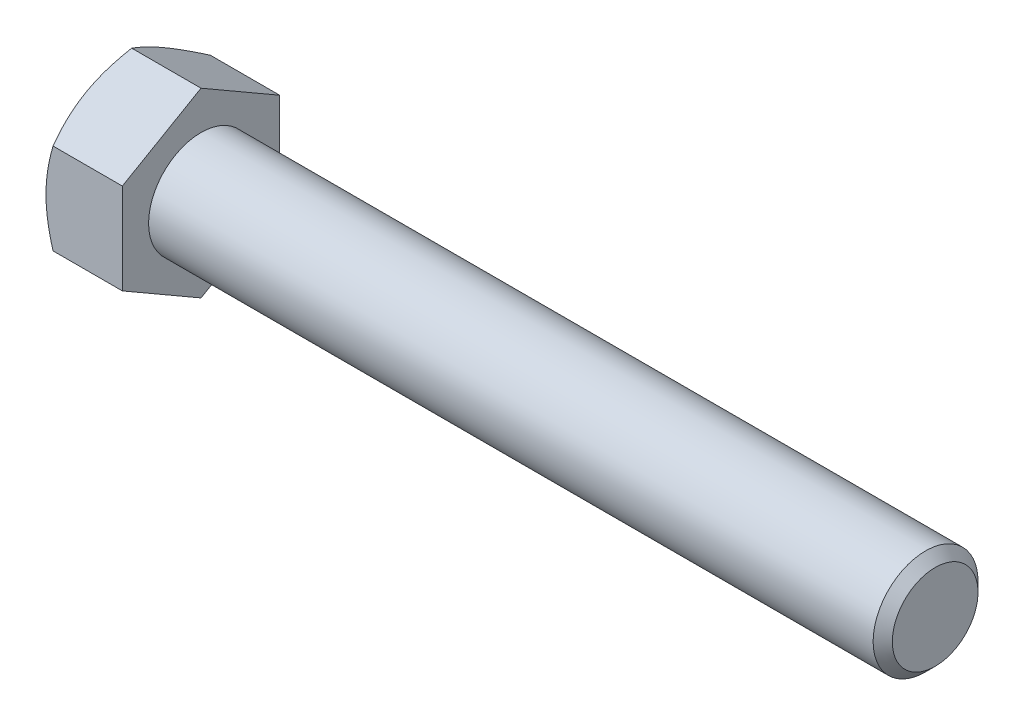
SolidWorks part; units mm, degrees
ref_plane "Plane1" through (0, 0, 0) normal (0, 0, 1) x (1, 0, 0)
ref_plane "Plane2" through (0, 0, 0) normal (0, 1, 0) x (1, 0, 0)
ref_plane "Plane3" through (0, 0, 0) normal (1, 0, 0) x (0, 0, -1)
sketch "Sketch1" plane through (0, 0, 0) normal (1, 0, 0) x (0, 0, -1)
  line L0 (9.525, 5.4993) -> (9.525, -5.4993)
  line L1 (-9.525, 5.4993) -> (-9.525, -5.4993)
  line L2 (9.525, -5.4993) -> (0, -10.9985)
  line L3 (0, -10.9985) -> (-9.525, -5.4993)
  line L4 (9.525, 5.4993) -> (0, 10.9985)
  line L5 (0, 10.9985) -> (-9.525, 5.4993)
  dimension "Width_flats" = 19.05
  dimension "D2" = 120
  dimension "D3" = 9.525
  dimension "D4" = 9.525
  dimension "D5" = 9.525
extrude "BaseHead" add sketch "Sketch1" along normal blind 9.2456
sketch "BodySke" plane through (0, 0, 0) normal (0, 0, 1) x (1, 0, 0)
  line L0 (0, 5.4993) -> (0, -5.4993) construction
  line L1 (0, 0) -> (98.1456, 0)
  line L2 (0, 0) -> (0, 6.35)
  line L3 (0, 6.35) -> (96.9823, 6.35)
  line L4 (98.1456, 0) -> (98.1456, 5.1867)
  line L5 (9.2456, 10.9985) -> (9.2456, 5.4993) construction
  line L6 (98.1456, 5.1867) -> (96.9823, 6.35)
  line L7 (0, 0) -> (96.52, 0) construction
  line L8 (98.1456, -5.1867) -> (96.9823, -6.35) construction
  line L9 (0, -6.35) -> (96.9823, -6.35) construction
  line L10 (11.1989, 15.24) -> (11.1989, -2.54) construction
  line L11 (66.3956, 15.24) -> (66.3956, -2.54) construction
  line L12 (9.2456, 5.4993) -> (9.2456, -5.4993) construction
  dimension "Length" = 88.9
  dimension "Body_ch_ang" = 45
  dimension "Diameter" = 12.7
  dimension "Minor_dia" = 10.3734
  dimension "Advance" = 1.9533
  dimension "Thread_nom" = 31.75
revolve "BaseBody" add sketch "BodySke" angle 360 about L7
cosmetic thread "ThreadCosmetic" parameters "Thread_length"=31.75, "Thread_minor"=10.3734
sketch "Sketch3" plane through (0, 0, 0) normal (0, 0, 1) x (1, 0, 0)
  line L0 (0, 9.525) -> (4.5169, 17.3485)
  line L1 (0, 10.9985) -> (0, 5.4993) construction
  line L2 (4.5169, 17.3485) -> (4.5169, 23.6985)
  line L3 (4.5169, 23.6985) -> (-12.7, 23.6985)
  line L4 (-12.7, 23.6985) -> (-12.7, 9.525)
  line L5 (-12.7, 9.525) -> (0, 9.525)
  line L6 (0, 0) -> (99.06, 0) construction
  line L7 (9.2456, 10.9985) -> (0, 10.9985) construction
  dimension "D1" = 9.525
  dimension "D2" = 6.35
  dimension "D3" = 12.7
  dimension "D4" = 6.35
  dimension "Head_ch_ang" = 30
revolve "HeadChamfer" cut sketch "Sketch3" angle 360 about L6
fillet "HeadFillet" [suppressed] radius 0.762
sketch "ThdSchSke" plane through (0, 0, 0) normal (0, 0, 1) x (1, 0, 0)
  line L0 (66.3956, -5.1867) -> (65.581, -6.35)
  line L1 (66.3956, -5.1867) -> (67.2102, -6.35)
  line L2 (67.2102, -6.35) -> (67.2102, -7.9375)
  line L3 (-3.175, 0) -> (5.1513, 0) construction
  line L5 (67.2102, -7.9375) -> (65.581, -7.9375)
  line L6 (65.581, -7.9375) -> (65.581, -6.35)
  dimension "Thread_minor" = 10.3734
  dimension "Diameter" = 12.7
  dimension "Start" = 66.3956
  dimension "SideAngle" = 55
  dimension "VeeAngle" = 70
  dimension "Overcut" = 15.875
revolve "ThreadSchematic" [suppressed] cut sketch "ThdSchSke" angle 360 about L3
pattern_linear "ThdSchPat" [suppressed]
equation "\"D3@Sketch1\" = \"Width_flats@Sketch1\" / 2"
equation "\"D4@Sketch1\" = \"D3@Sketch1\""
equation "\"D5@Sketch1\" = \"D4@Sketch1\""
equation "\"Thread_minor@ThreadCosmetic\" = \"Minor_dia@BodySke\""
equation "\"D1@Sketch3\" = \"Width_flats@Sketch1\" / 2"
equation "\"Thread_length@ThreadCosmetic\" = ((sgn( (\"Length@BodySke\" - \"Advance@BodySke\" ) - \"Thread_nom@BodySke\" )-1)*( (\"Length@BodySke\" - \"Advance@BodySke\" ) - \"Thread_nom@BodySke\" ))/-2+ \"Thread_nom@BodySke\""
equation "\"Thread_minor@ThdSchSke\" = \"Minor_dia@BodySke\""
equation "\"Diameter@ThdSchSke\" = \"Diameter@BodySke\""
equation "\"Overcut@ThdSchSke\" = \"Diameter@BodySke\" * 1.25"
equation "\"Start@ThdSchSke\" = \"Head_ht@BaseHead\" + \"Length@BodySke\" - \"Thread_length@ThreadCosmetic\"  '---Non-countersunk---"
equation "\"Num_threads@ThdSchPat\" = int( \"Thread_length@ThreadCosmetic\" / \"Advance@BodySke\" + 0.999 )  + 1"
equation "\"Advance@ThdSchPat\" = \"Thread_length@ThreadCosmetic\" /  (\"Num_threads@ThdSchPat\" - 1) 'relax it"
equation "\"Num_threads@ThdSchPat\" = \"Num_threads@ThdSchPat\" - sgn( \"Num_threads@ThdSchPat\" - 1) '---chamfered tips only---"
